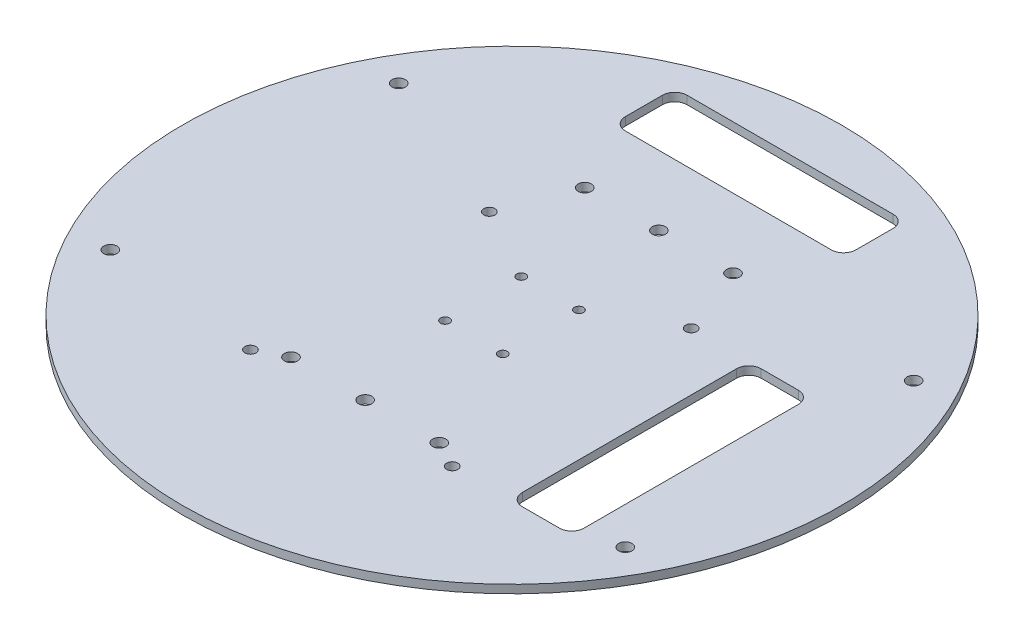
SolidWorks part; units mm, degrees
ref_plane "前视基准面" through (0, 0, 0) normal (0, 0, 1) x (1, 0, 0)
ref_plane "上视基准面" through (0, 0, 0) normal (0, 1, 0) x (1, 0, 0)
ref_plane "右视基准面" through (0, 0, 0) normal (1, 0, 0) x (0, 0, -1)
sketch "草图1" plane through (0, 0, 0) normal (0, 1, 0) x (1, 0, 0)
  circle A0 centre (0, 0) radius 80
  dimension "D1" = 160
extrude "凸台-拉伸1" add sketch "草图1" along normal blind 2 contours A0
sketch "草图2" plane through (0, 2, 0) normal (0, 1, 0) x (1, 0, 0)
  line L0 (0, 0) -> (0, 22.3819) construction
  line L1 (-62.5, 35) -> (62.5, 35) construction
  line L2 (-62.5, 35) -> (-62.5, -35) construction
  line L3 (-62.5, -35) -> (62.5, -35) construction
  line L4 (62.5, 35) -> (62.5, -35) construction
  line L5 (-62.5, 35) -> (62.5, -35) construction
  line L6 (-62.5, -35) -> (62.5, 35) construction
  circle A0 centre (-62.5, 35) radius 1.6
  circle A1 centre (-62.5, -35) radius 1.6
  circle A2 centre (62.5, -35) radius 1.6
  circle A3 centre (62.5, 35) radius 1.6
  point P0 (0, 0)
  dimension "D3" = 3.2
  dimension "D4" = 3.2
  dimension "D1" = 125
  dimension "D2" = 70
extrude "上下板连接孔位" cut sketch "草图2" against normal blind 2
sketch "草图3" plane through (0, 2, 0) normal (0, 1, 0) x (1, 0, 0)
  line L0 (0, -42.5) -> (0, -39) construction
  line L5 (0, 52.5) -> (0, 42.5) construction
  line L7 (-28, 42.5) -> (28, 42.5) construction
  line L8 (-28, 42.5) -> (-28, -42.5) construction
  line L9 (-28, -42.5) -> (28, -42.5) construction
  line L10 (28, 42.5) -> (28, -42.5) construction
  line L11 (-28, 42.5) -> (28, -42.5) construction
  line L12 (-28, -42.5) -> (28, 42.5) construction
  line L13 (-24.5, 19) -> (24.5, 19) construction
  line L14 (-24.5, 19) -> (-24.5, -39) construction
  line L15 (-24.5, -39) -> (24.5, -39) construction
  line L16 (24.5, 19) -> (24.5, -39) construction
  line L17 (24.5, -10) -> (38.5, -10) construction
  line L18 (-28, 67.5) -> (28, 67.5)
  line L19 (-28, 67.5) -> (-28, 52.5)
  line L20 (-28, 52.5) -> (28, 52.5)
  line L21 (28, 67.5) -> (28, 52.5)
  line L23 (38.5, 19) -> (53.5, 19)
  line L24 (38.5, 19) -> (38.5, -39)
  line L25 (38.5, -39) -> (53.5, -39)
  line L26 (53.5, 19) -> (53.5, -39)
  circle A0 centre (-24.5, 19) radius 1.35
  circle A1 centre (-24.5, -39) radius 1.35
  circle A2 centre (24.5, -39) radius 1.35
  circle A3 centre (24.5, 19) radius 1.35
  point P1 (0, 0)
  point P12 (0, -39)
  point P17 (0, 42.5)
  point P18 (0, 52.5)
  point P25 (0, 52.5)
  point P27 (24.5, -10)
  point P33 (38.5, -10)
  dimension "D3" = 49
  dimension "D4" = 58
  dimension "D5" = 3.5
  dimension "D6" = 2.7
  dimension "D7" = 2.7
  dimension "D1" = 56
  dimension "D2" = 85
  dimension "D8" = 10
  dimension "D9" = 56
  dimension "D10" = 15
  dimension "D11" = 14
  dimension "D12" = 15
  dimension "D13" = 58
extrude "树莓派孔位" cut sketch "草图3" against normal blind 2
sketch "草图4" plane through (0, 2, 0) normal (0, 1, 0) x (1, 0, 0)
  line L0 (0, 0) -> (10.9639, 0) construction
  line L1 (-18, 35.65) -> (18, 35.65) construction
  line L2 (-18, 35.65) -> (-18, -35.65) construction
  line L3 (-18, -35.65) -> (18, -35.65) construction
  line L4 (18, 35.65) -> (18, -35.65) construction
  line L5 (-18, 35.65) -> (18, -35.65) construction
  line L6 (-18, -35.65) -> (18, 35.65) construction
  circle A0 centre (-18, 35.65) radius 1.6
  circle A1 centre (0, 35.65) radius 1.6
  circle A2 centre (18, 35.65) radius 1.6
  circle A3 centre (18, -35.65) radius 1.6
  circle A4 centre (0, -35.65) radius 1.6
  circle A5 centre (-18, -35.65) radius 1.6
  point P0 (0, 0)
  point P6 (0, 35.65)
  dimension "D3" = 3.2
  dimension "D4" = 3.2
  dimension "D5" = 3.2
  dimension "D1" = 71.3
  dimension "D2" = 36
extrude "雷达孔位" cut sketch "草图4" against normal blind 2
sketch "草图5" plane through (0, 2, 0) normal (0, 1, 0) x (1, 0, 0)
  line L0 (0, 0) -> (32.0565, 0) construction
  line L1 (-7, 9.25) -> (7, 9.25) construction
  line L2 (-7, 9.25) -> (-7, -9.25) construction
  line L3 (-7, -9.25) -> (7, -9.25) construction
  line L4 (7, 9.25) -> (7, -9.25) construction
  line L5 (-7, 9.25) -> (7, -9.25) construction
  line L6 (-7, -9.25) -> (7, 9.25) construction
  circle A0 centre (-7, 9.25) radius 1.1
  circle A1 centre (7, 9.25) radius 1.1
  circle A2 centre (7, -9.25) radius 1.1
  circle A3 centre (-7, -9.25) radius 1.1
  point P0 (0, 0)
  dimension "D1" = 2.2
  dimension "D2" = 2.2
  dimension "D3" = 14
  dimension "D4" = 18.5
extrude "串口转接板孔位" cut sketch "草图5" against normal blind 2
fillet "圆角2" radius 3 8 edges at (38.5, 1, 39) (53.5, 1, 39) (53.5, 1, -19) (38.5, 1, -19) (-28, 1, -52.5) (-28, 1, -67.5) (28, 1, -52.5) (28, 1, -67.5)
